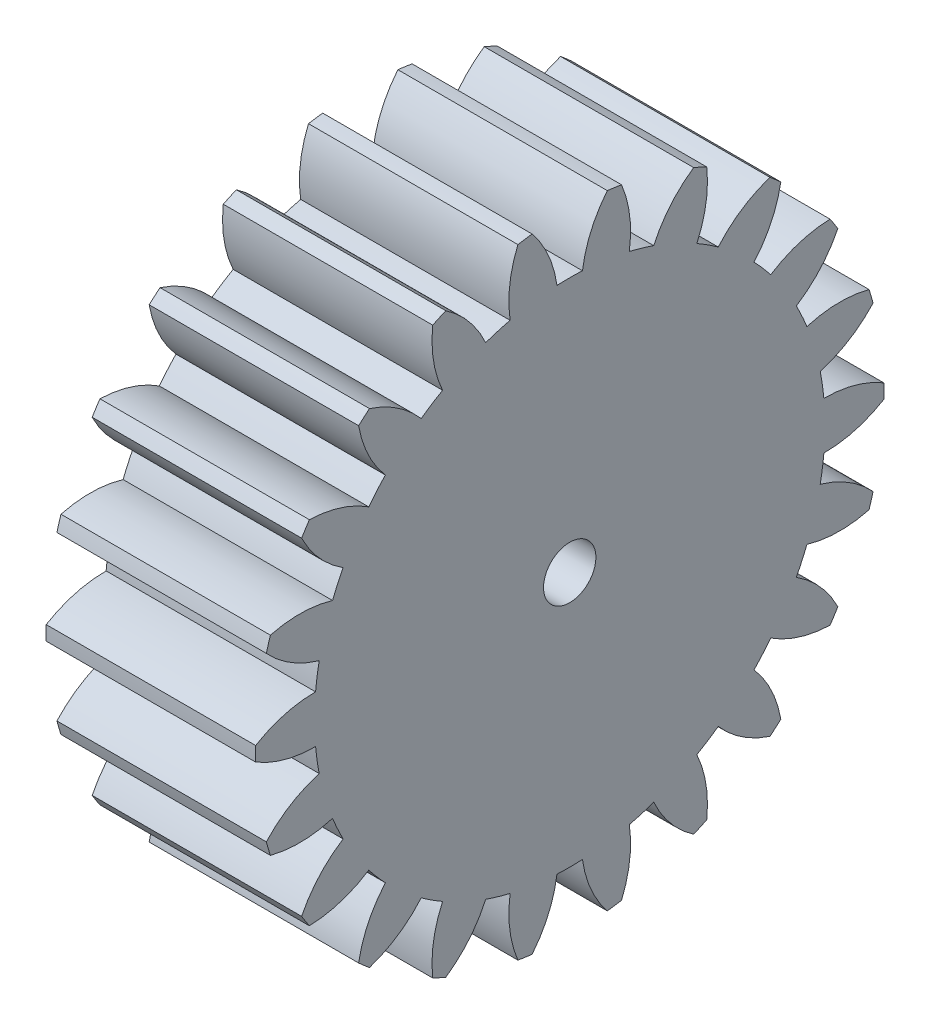
SolidWorks part; units mm, degrees
ref_plane "Plane1" through (0, 0, 0) normal (0, 0, 1) x (1, 0, 0)
ref_plane "Plane2" through (0, 0, 0) normal (0, 1, 0) x (1, 0, 0)
ref_plane "Plane3" through (0, 0, 0) normal (1, 0, 0) x (0, 0, -1)
sketch "HoldingSke" plane through (0, 0, 0) normal (0, 1, 0) x (1, 0, 0)
  line L0 (0, 0) -> (0.3709, -0.1498)
  line L1 (-15, 0) -> (100, 0) construction
  line L2 (0, 0) -> (-2.1039, 2.3779)
  line L3 (0, 0) -> (-11.863, 4.5341)
  line L4 (0, 0) -> (8.0072, 3.2351)
  line L5 (0, 0) -> (-46.8476, -17.4728)
  line L6 (0, 0) -> (-16.5793, -11.1861)
  line L7 (-2.1039, 2.3779) -> (8.6586, 51.2059)
  line L8 (-76.2, 54.61) -> (-75.3, 54.61)
  line L9 (-71.009, 38.7566) -> (-53.1078, 45.2721)
  line L10 (-76.2, 71.12) -> (104.1128, 71.12)
  line L11 (0, 0) -> (-20, 0)
  line L12 (-76.2, 101.6) -> (-76.113, 101.6)
  line L13 (24.9733, 27.94) -> (52.9518, 28.4284)
  line L14 (24.9733, 27.94) -> (24.9743, 27.94)
  line L15 (24.9733, 27.94) -> (100.4006, 29.5858)
  line L16 (-63.627, -2.5) -> (-12.827, -2.5)
  circle A0 centre (0, 0) radius 2.5
  circle A1 centre (0, 0) radius 24.374
  circle A2 centre (0, 0) radius 37.5
  circle A3 centre (0, 0) radius 2.5
  dimension "MHD" = 48.748
  dimension "Hub_dia" = 75
  dimension "Bore" = 5
  dimension "MBD" = 5
  dimension "Num_teeth" = 22
  dimension "Pitch" = 0.4
  dimension "Overall_len" = 50
  dimension "Show_teeth" = 22
  dimension "Thickness" = 20
  dimension "OAL" = 50.0001
  dimension "T_dim" = 0.9
  dimension "Ap" = 20
  dimension "H" = 19.05
  dimension "Pitch_radius" = 180.3128
  dimension "Width" = 20
  dimension "Backlash" = 0.087
  dimension "Addendum_fac" = 1
  dimension "Dedendum_fac" = 1.25
  dimension "Clearance_fac" = 0.25
  dimension "Dedendum_add" = 0.001
  dimension "Module" = 2.5
sketch "BasProSke" plane through (0, 0, 0) normal (0, 1, 0) x (1, 0, 0)
  line L0 (-10, 0) -> (60, 0) construction
  line L1 (0, 0) -> (0, 30)
  line L2 (0, 0) -> (20, 0)
  line L3 (20, 0) -> (20, 30)
  line L4 (20, 30) -> (0, 30)
  dimension "Thickness" = 20
  dimension "Diameter" = 60
revolve "Base-Revolve" add sketch "BasProSke" angle 360 about L0
sketch "TooCutSke" plane through (0, 0, 0) normal (1, 0, 0) x (0, 0, -1)
  line L1 (0, 0) -> (0, 107) construction
  line L2 (0, 0) -> (-2.114, 27.4186) construction
  line L3 (0, 0) -> (-7.8104, 54.3222) construction
  line L4 (-2.114, 27.4186) -> (-3.9052, 27.1611) construction
  arc A0 (1.2153, 24.3437) -> (-1.2153, 24.3437) centre (0, 0) ccw
  arc A1 (3.6084, 29.8078) -> (-3.6084, 29.8078) centre (0, 0) ccw
  circle A2 centre (0, 0) radius 27.5 construction
  circle A3 centre (0, 0) radius 25.8415 construction
  arc A4 (-1.2153, 24.3437) -> (-3.6084, 29.8078) centre (-12.1104, 22.8281) ccw
  arc A5 (3.6084, 29.8078) -> (1.2153, 24.3437) centre (12.1104, 22.8281) ccw
  dimension "Root_dia" = 48.748
  dimension "Overcut_dia" = 60.0508
  dimension "Pitch_dia" = 55
  dimension "Base_dia" = 51.6831
  dimension "Flank_rad" = 11
  dimension "Half_ang" = 8.182
  dimension "Half_CT" = 1.8096
extrude "ToothCut" cut sketch "TooCutSke" along normal through all
fillet "Breaks" [suppressed] radius 0.05
fillet "RootFillets" [suppressed] radius 0.626
pattern_circular "TeethCuts" count 22 every 16.364 about axis through (-10, 0, 0) along (1, 0, 0) of "ToothCut", "RootFillets", "Breaks"
sketch "HubNeaOneSke" plane through (0, 0, 0) normal (-1, 0, 0) x (0, 0, 1)
  circle A0 centre (0, 0) radius 24.374
  dimension "Diameter" = 48.748
extrude "HubNearOne" [suppressed] add sketch "HubNeaOneSke" along normal blind 30.0001
sketch "HubNeaBotSke" plane through (0, 0, 0) normal (-1, 0, 0) x (0, 0, 1)
  circle A0 centre (0, 0) radius 24.374
  dimension "Diameter" = 48.748
extrude "HubNearBoth" [suppressed] add sketch "HubNeaBotSke" along normal blind 15
ref_plane "FarPln" through (20, 0, 0) normal (1, 0, 0) x (0, 0, -1)
sketch "HubFarSke" plane through (20, 0, 0) normal (1, 0, 0) x (0, 0, -1)
  circle A0 centre (0, 0) radius 24.374
  dimension "Diameter" = 48.748
extrude "HubFar" [suppressed] add sketch "HubFarSke" along normal blind 15
sketch "BorSke" plane through (0, 0, 0) normal (1, 0, 0) x (0, 0, -1)
  circle A0 centre (0, 0) radius 2.5
  dimension "Diameter" = 5
extrude "Bore" cut sketch "BorSke" along normal mid plane 100.0001
sketch "KeySke" plane through (0, 0, 0) normal (1, 0, 0) x (0, 0, -1)
  line L0 (-1, 0) -> (-1, 3.4)
  line L1 (-1, 3.4) -> (1, 3.4)
  line L2 (1, 3.4) -> (1, 0)
  line L3 (0, 0) -> (0, 34) construction
  line L4 (-1, 0) -> (1, 0)
  dimension "Offset" = 3.4
extrude "Keyway" [suppressed] cut sketch "KeySke" along normal mid plane 100.0001
pattern_circular "Keyway2" [suppressed] count 2 every 90 about axis through (-10, 0, 0) along (1, 0, 0)
equation "' \"Module@HoldingSke\" = 6.35"
equation "' \"Num_teeth@HoldingSke\" = 12"
equation "' \"Ap@HoldingSke\" =  20"
equation "' \"Ap@HoldingSke\" = 20"
equation "' \"Width@HoldingSke\" = 0.5 * 25.4"
equation "' \"Hub_dia@HoldingSke\"= 1 * 25.4"
equation "' \"Hub_dia@HoldingSke\" = 1 * 25.4"
equation "' \"Overall_len@HoldingSke\" = 1.0 * 25.4"
equation "' \"Bore@HoldingSke\" = 0.75 * 25.4"
equation "' \"T_dim@HoldingSke\" = 0.1 * 25.4"
equation "' \"Width@KeySke\" = 0.25 * 25.4"
equation "' \"Show_teeth@HoldingSke\" = 13"
equation "' \"Backlash@HoldingSke\" = 0.009 * 25.4"
equation "' \"Addendum_fac@HoldingSke\" = 1.0"
equation "' \"Dedendum_fac@HoldingSke\" = 1.25"
equation "' \"Dedendum_add@HoldingSke\" = 0.00005 * 25.4"
equation "' \"Clearance_fac@HoldingSke\" = 0.25"
equation "\"Pitch@HoldingSke\" = 1 / \"Module@HoldingSke\""
equation "\"Overcut_dia@TooCutSke\" = (\"Num_teeth@HoldingSke\" + 2 * \"Addendum_fac@HoldingSke\") / \"Pitch@HoldingSke\" + 0.002 * 25.4"
equation "\"Pitch_dia@TooCutSke\" = \"Num_teeth@HoldingSke\" / \"Pitch@HoldingSke\""
equation "\"Base_dia@TooCutSke\" = \"Num_teeth@HoldingSke\" / \"Pitch@HoldingSke\" * cos((\"Ap@HoldingSke\"  * 3.14159265 / 180))"
equation "\"Root_dia@TooCutSke\" = (\"Num_teeth@HoldingSke\" + 2) / \"Pitch@HoldingSke\" - 2 * (\"Addendum_fac@HoldingSke\" + \"Dedendum_fac@HoldingSke\") / \"Pitch@HoldingSke\" - \"Dedendum_add@HoldingSke\" * 2"
equation "\"Half_ang@TooCutSke\" = 180 / \"Num_teeth@HoldingSke\""
equation "\"Half_CT@TooCutSke\" = \"Num_teeth@HoldingSke\" / \"Pitch@HoldingSke\" * sin((3.14159265 / 2 / \"Num_teeth@HoldingSke\")) / 2 - 7 * \"Backlash@HoldingSke\" / 4"
equation "\"Flank_rad@TooCutSke\" = \"Num_teeth@HoldingSke\" / \"Pitch@HoldingSke\" / 5"
equation "\"Radius@RootFillets\" = \"Clearance_fac@HoldingSke\" / \"Pitch@HoldingSke\" + \"Dedendum_add@HoldingSke\""
equation "\"Break_rad@Breaks\" = 0.02 / \"Pitch@HoldingSke\""
equation "\"Thickness@HoldingSke\" = \"Width@HoldingSke\""
equation "\"OAL@HoldingSke\" = \"Thickness@HoldingSke\""
equation "\"MHD@HoldingSke\" = (\"Num_teeth@HoldingSke\" + 2) / \"Pitch@HoldingSke\" - 2 * (\"Addendum_fac@HoldingSke\" + \"Dedendum_fac@HoldingSke\")  / \"Pitch@HoldingSke\" - \"Dedendum_add@HoldingSke\" * 2"
equation "\"MBD@HoldingSke\" = (\"Num_teeth@HoldingSke\" + 2) / \"Pitch@HoldingSke\" - 2 * (\"Addendum_fac@HoldingSke\" + \"Dedendum_fac@HoldingSke\")  / \"Pitch@HoldingSke\" - \"Dedendum_add@HoldingSke\" * 2 - 0.002 * 25.4"
equation "\"MHD@HoldingSke\" = ((sgn( \"MHD@HoldingSke\" - \"Hub_dia@HoldingSke\" )-1)*( \"MHD@HoldingSke\" - \"Hub_dia@HoldingSke\" ))/-2+ \"Hub_dia@HoldingSke\""
equation "\"MBD@HoldingSke\" = ((sgn( \"MBD@HoldingSke\" - \"Bore@HoldingSke\" )-1)*( \"MBD@HoldingSke\" - \"Bore@HoldingSke\" ))/-2+ \"Bore@HoldingSke\""
equation "\"OAL@HoldingSke\" = ((sgn( \"OAL@HoldingSke\" - \"Overall_len@HoldingSke\" )+1)*( \"OAL@HoldingSke\" - \"Overall_len@HoldingSke\" ))/2 + \"Overall_len@HoldingSke\" + 0.000002 * 25.4"
equation "\"Num_teeth@TeethCuts\" = int( \"Show_teeth@HoldingSke\" ) + 1"
equation "\"Num_teeth@TeethCuts\" = ((sgn( \"Num_teeth@TeethCuts\" - \"Num_teeth@HoldingSke\" )-1)*( \"Num_teeth@TeethCuts\" - \"Num_teeth@HoldingSke\" ))/-2+ \"Num_teeth@HoldingSke\""
equation "\"Num_teeth@TeethCuts\" = ((sgn( \"Num_teeth@TeethCuts\" - 2.0)+1)*( \"Num_teeth@TeethCuts\" - 2.0))/2 +2.0"
equation "\"Angle@TeethCuts\" = 360.0 / \"Num_teeth@HoldingSke\""
equation "\"Diameter@BasProSke\" = (\"Num_teeth@HoldingSke\" + 2 * \"Addendum_fac@HoldingSke\") / \"Pitch@HoldingSke\""
equation "\"Thickness@BasProSke\"  = \"Thickness@HoldingSke\""
equation "' \"Fillet_rad@BasProSke\" =  \"Thickness@HoldingSke\" * 0.05"
equation "' \"Fillet_rad@BasProSke\" = \"Thickness@HoldingSke\" * 0.05"
equation "\"MHD@HoldingSke\" = ((sgn( \"MHD@HoldingSke\" - \"Root_dia@TooCutSke\" )-1)*( \"MHD@HoldingSke\" - \"Root_dia@TooCutSke\" ))/-2+ \"Root_dia@TooCutSke\""
equation "\"Diameter@HubNeaOneSke\" = \"MHD@HoldingSke\""
equation "\"Length@HubNearOne\" = \"OAL@HoldingSke\" - \"Thickness@BasProSke\""
equation "\"Diameter@HubNeaBotSke\" = \"MHD@HoldingSke\""
equation "\"Length@HubNearBoth\" = ( \"OAL@HoldingSke\" - \"Thickness@BasProSke\" ) / 2.0"
equation "\"Thickness@FarPln\" = \"Thickness@BasProSke\""
equation "\"Diameter@HubFarSke\" = \"MHD@HoldingSke\""
equation "\"Length@HubFar\" = ( \"OAL@HoldingSke\" - \"Thickness@BasProSke\" ) / 2.0"
equation "\"Diameter@BorSke\" = \"MBD@HoldingSke\""
equation "\"D1@Bore\" = \"OAL@HoldingSke\" * 2.0"
equation "\"D1@Keyway\" = \"OAL@HoldingSke\" * 2.0"
equation "\"Offset@KeySke\" = \"T_dim@HoldingSke\" + \"MBD@HoldingSke\" / 2.0"
